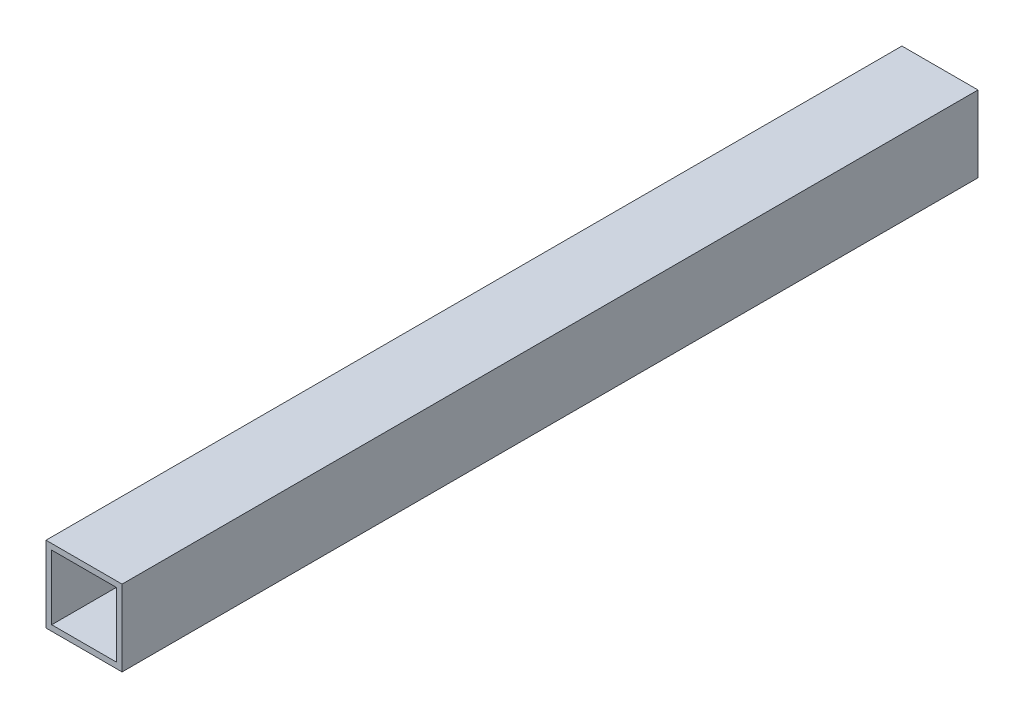
SolidWorks part; units mm, degrees
ref_plane "Alzado" through (0, 0, 0) normal (0, 0, 1) x (1, 0, 0)
ref_plane "Planta" through (0, 0, 0) normal (0, 1, 0) x (1, 0, 0)
ref_plane "Vista lateral" through (0, 0, 0) normal (1, 0, 0) x (0, 0, -1)
sketch "Croquis1" plane through (0, 0, 0) normal (0, 0, 1) x (1, 0, 0)
  line L0 (-17, 17) -> (17, 17)
  line L1 (-20, 20) -> (20, 20)
  line L2 (-20, 20) -> (-20, -20)
  line L3 (-20, -20) -> (20, -20)
  line L4 (20, 20) -> (20, -20)
  line L5 (-20, 20) -> (20, -20) construction
  line L6 (-20, -20) -> (20, 20) construction
  line L7 (17, 17) -> (17, -17)
  line L8 (-17, -17) -> (17, -17)
  line L9 (-17, 17) -> (-17, -17)
  point P0 (0, 0)
  dimension "D1" = 3
extrude "Saliente-Extruir1" add sketch "Croquis1" along normal blind 450
